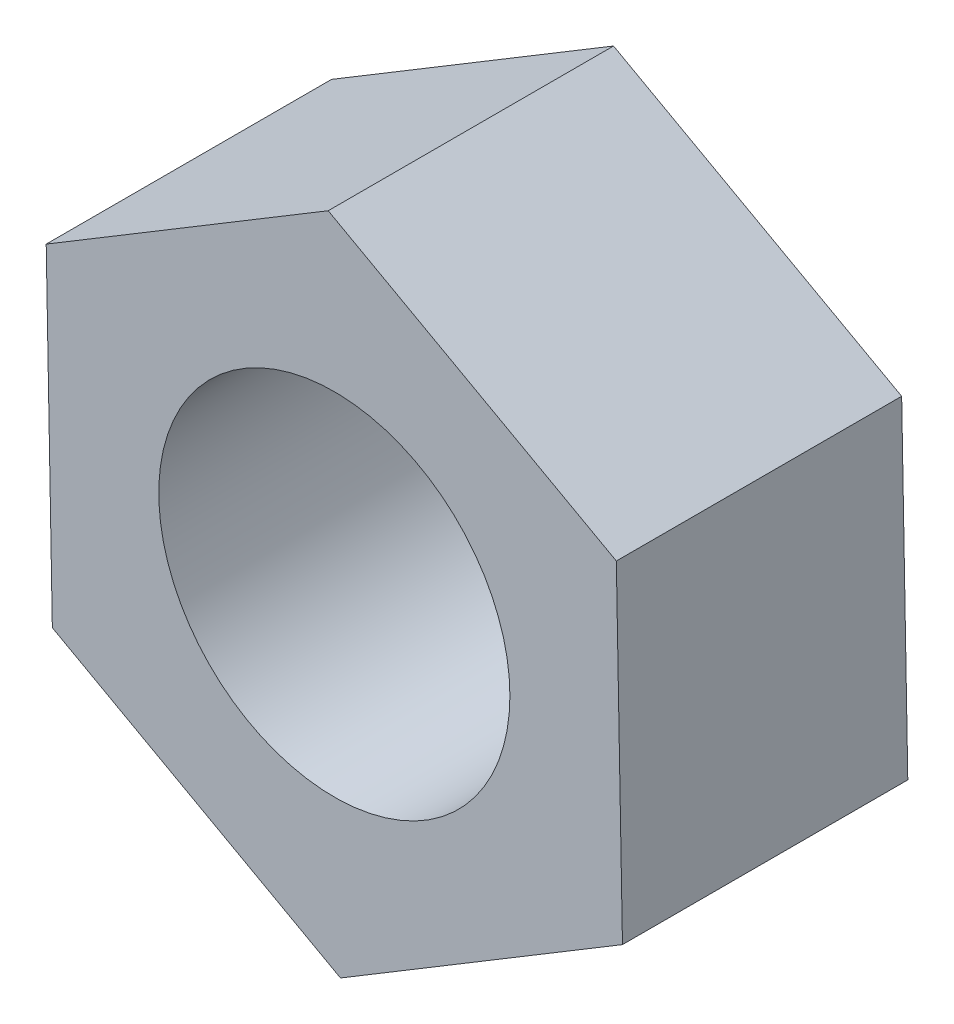
SolidWorks part; units mm, degrees
ref_plane "Front Plane" through (0, 0, 0) normal (0, 0, 1) x (1, 0, 0)
ref_plane "Top Plane" through (0, 0, 0) normal (0, 1, 0) x (1, 0, 0)
ref_plane "Right Plane" through (0, 0, 0) normal (1, 0, 0) x (0, 0, -1)
sketch "Sketch1" plane through (0, 0, 0) normal (0, 0, 1) x (1, 0, 0)
  line L1 (-6.564, 3.6282) -> (-6.4241, -3.8705)
  line L2 (-6.4241, -3.8705) -> (0.1399, -7.4987)
  line L3 (0.1399, -7.4987) -> (6.564, -3.6282)
  line L4 (6.564, -3.6282) -> (6.4241, 3.8705)
  line L5 (6.4241, 3.8705) -> (-0.1399, 7.4987)
  line L6 (-0.1399, 7.4987) -> (-6.564, 3.6282)
  circle A0 centre (0, 0) radius 7.5 construction
  circle A1 centre (0, 0) radius 4
  dimension "D1" = 15
  dimension "D2" = 8
extrude "Boss-Extrude1" add sketch "Sketch1" along normal blind 6.5
